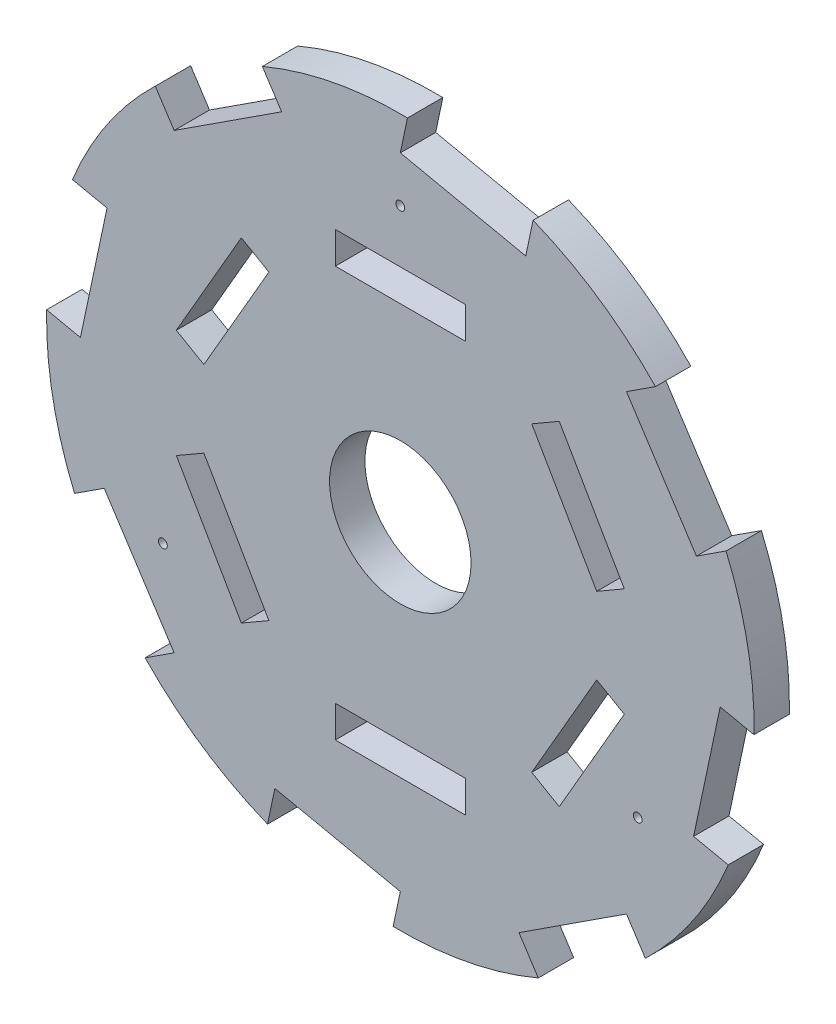
SolidWorks part; units mm, degrees
ref_plane "Ebene vorne" through (0, 0, 0) normal (0, 0, 1) x (1, 0, 0)
ref_plane "Ebene oben" through (0, 0, 0) normal (0, 1, 0) x (1, 0, 0)
ref_plane "Ebene rechts" through (0, 0, 0) normal (1, 0, 0) x (0, 0, -1)
sketch "Skizze1" plane through (0, 0, 0) normal (0, 0, 1) x (1, 0, 0)
  line L0 (0, 36.1689) -> (14.1846, 33.1623)
  line L1 (0, 36.1689) -> (0.8103, 39.9918)
  line L2 (14.1846, 33.1623) -> (15.014, 37.0753)
  line L5 (25.5753, 25.5753) -> (28.8515, 27.7055)
  line L6 (25.5753, 25.5753) -> (33.4793, 13.4193)
  line L7 (33.4793, 13.4193) -> (36.8327, 15.5997)
  line L9 (36.1689, 0) -> (39.9918, -0.8103)
  line L10 (36.1689, 0) -> (33.1623, -14.1846)
  line L11 (33.1623, -14.1846) -> (37.0753, -15.014)
  line L13 (25.5753, -25.5753) -> (27.7055, -28.8515)
  line L14 (25.5753, -25.5753) -> (13.4193, -33.4793)
  line L15 (13.4193, -33.4793) -> (15.5997, -36.8327)
  line L17 (0, -36.1689) -> (-0.8103, -39.9918)
  line L18 (0, -36.1689) -> (-14.1846, -33.1623)
  line L19 (-14.1846, -33.1623) -> (-15.014, -37.0753)
  line L21 (-25.5753, -25.5753) -> (-28.8515, -27.7055)
  line L22 (-25.5753, -25.5753) -> (-33.4793, -13.4193)
  line L23 (-33.4793, -13.4193) -> (-36.8327, -15.5997)
  line L25 (-36.1689, 0) -> (-39.9918, 0.8103)
  line L26 (-36.1689, 0) -> (-33.1623, 14.1846)
  line L27 (-33.1623, 14.1846) -> (-37.0753, 15.014)
  line L29 (-25.5753, 25.5753) -> (-27.7055, 28.8515)
  line L30 (-25.5753, 25.5753) -> (-13.4193, 33.4793)
  line L31 (-13.4193, 33.4793) -> (-15.5997, 36.8327)
  arc A0 (0.8103, 39.9918) -> (-15.5997, 36.8327) centre (0, 0) ccw
  arc A2 (28.8515, 27.7055) -> (15.014, 37.0753) centre (0, 0) ccw
  arc A4 (39.9918, -0.8103) -> (36.8327, 15.5997) centre (0, 0) ccw
  arc A6 (27.7055, -28.8515) -> (37.0753, -15.014) centre (0, 0) ccw
  arc A8 (-0.8103, -39.9918) -> (15.5997, -36.8327) centre (0, 0) ccw
  arc A10 (-28.8515, -27.7055) -> (-15.014, -37.0753) centre (0, 0) ccw
  arc A12 (-39.9918, 0.8103) -> (-36.8327, -15.5997) centre (0, 0) ccw
  arc A14 (-27.7055, 28.8515) -> (-37.0753, 15.014) centre (0, 0) ccw
  point P38 (0, 0)
  dimension "D1" = 80
  dimension "D2" = 4
  dimension "D3" = 14.5
  dimension "D4" = 8
extrude "Aufsatz-Linear austragen1" add sketch "Skizze1" along normal blind 4 contours L30 L31 A0 L1 L0 L2 A2 L5 L6 L7 A4 L9 L10 L11 A6 L13 L14 L15 A8 L17 L18 L19 A10 L21 L22 L23 A12 L25 L26 L27 A14 L29
sketch "Skizze2" plane through (0, 0, 4) normal (0, 0, 1) x (1, 0, 0)
  circle A0 centre (0, 0) radius 8
  dimension "D1" = 16
extrude "Schnitt-Linear austragen1" cut sketch "Skizze2" against normal up to next
sketch "Skizze3" plane through (0, 0, 0) normal (1, 0, 0) x (0, 0, -1)
  line L0 (-9.579, 0) -> (9.5433, 0) construction
sketch "Skizze4" plane through (0, 0, 4) normal (0, 0, 1) x (1, 0, 0)
  line L1 (-7.35, 21.4) -> (7.35, 21.4)
  line L2 (-7.35, 21.4) -> (-7.35, 25)
  line L3 (-7.35, 25) -> (7.35, 25)
  line L4 (7.35, 21.4) -> (7.35, 25)
  line L5 (-7.35, 21.4) -> (7.35, 25) construction
  line L6 (-7.35, 25) -> (7.35, 21.4) construction
  arc A0 (0.8103, 39.9918) -> (-15.5997, 36.8327) centre (0, 0) ccw construction
  point P0 (0, 23.2)
  dimension "D1" = 3.6
  dimension "D2" = 14.7
  dimension "D3" = 25
extrude "Schnitt-Linear austragen2" cut sketch "Skizze4" against normal up to next (4 mm away)
pattern_circular "Kreismuster1" count 6 over 360 about axis through (0, 0, 0) along (0, 0, 1) of "Schnitt-Linear austragen2"
sketch "Skizze5" plane through (0, 0, 4) normal (0, 0, 1) x (1, 0, 0)
  circle A0 centre (0, 31) radius 0.5
  dimension "D1" = 1
  dimension "D2" = 31
extrude "Schnitt-Linear austragen3" cut sketch "Skizze5" against normal up to next (4 mm away)
pattern_circular "Kreismuster2" count 3 over 360 about axis through (0, 0, 0) along (0, 0, 1) of "Schnitt-Linear austragen3"
